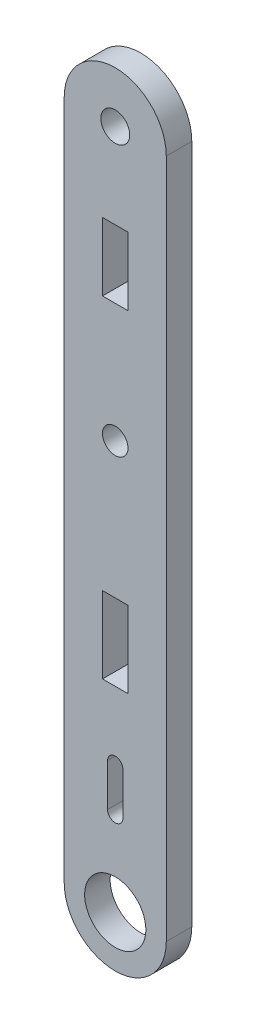
SolidWorks part; units mm, degrees
ref_plane "Front Plane" through (0, 0, 0) normal (0, 0, 1) x (1, 0, 0)
ref_plane "Top Plane" through (0, 0, 0) normal (0, 1, 0) x (1, 0, 0)
ref_plane "Right Plane" through (0, 0, 0) normal (1, 0, 0) x (0, 0, -1)
sketch "Model" plane through (0, 0, 0) normal (0, 0, 1) x (1, 0, 0)
  line L0 (39.519, 20.3523) -> (39.519, 75.7731)
  line L1 (39.519, 6.6775) -> (39.519, 20.3523)
  line L2 (27.519, 86.6776) -> (27.519, 6.6775)
  line L3 (39.519, 75.7731) -> (39.519, 86.6775)
  line L4 (32.019, 29.6775) -> (32.019, 38.6775)
  line L5 (35.019, 29.6775) -> (32.019, 29.6775)
  line L6 (35.019, 38.6775) -> (35.019, 29.6775)
  line L7 (32.019, 38.6775) -> (35.019, 38.6775)
  line L8 (32.019, 76.6775) -> (32.019, 68.6775)
  line L9 (35.019, 76.6775) -> (32.019, 76.6775)
  line L10 (35.019, 68.6775) -> (35.019, 76.6775)
  line L11 (32.019, 68.6775) -> (35.019, 68.6775)
  line L12 (32.619, 21.6776) -> (32.619, 16.6775)
  line L13 (34.419, 16.6775) -> (34.419, 21.6775)
  circle A0 centre (33.519, 6.6775) radius 3.6
  circle A1 centre (33.519, 86.6775) radius 1.7
  circle A2 centre (33.519, 54.6776) radius 1.5
  arc A3 (27.519, 6.6775) -> (39.519, 6.6775) centre (33.519, 6.6775) ccw
  arc A4 (39.519, 86.6775) -> (27.519, 86.6776) centre (33.519, 86.6776) ccw
  arc A5 (32.619, 16.6775) -> (34.419, 16.6775) centre (33.519, 16.6775) ccw
  arc A6 (34.419, 21.6775) -> (32.619, 21.6776) centre (33.519, 21.6776) ccw
extrude "Boss-Extrude1" add sketch "Model" along normal blind 3
